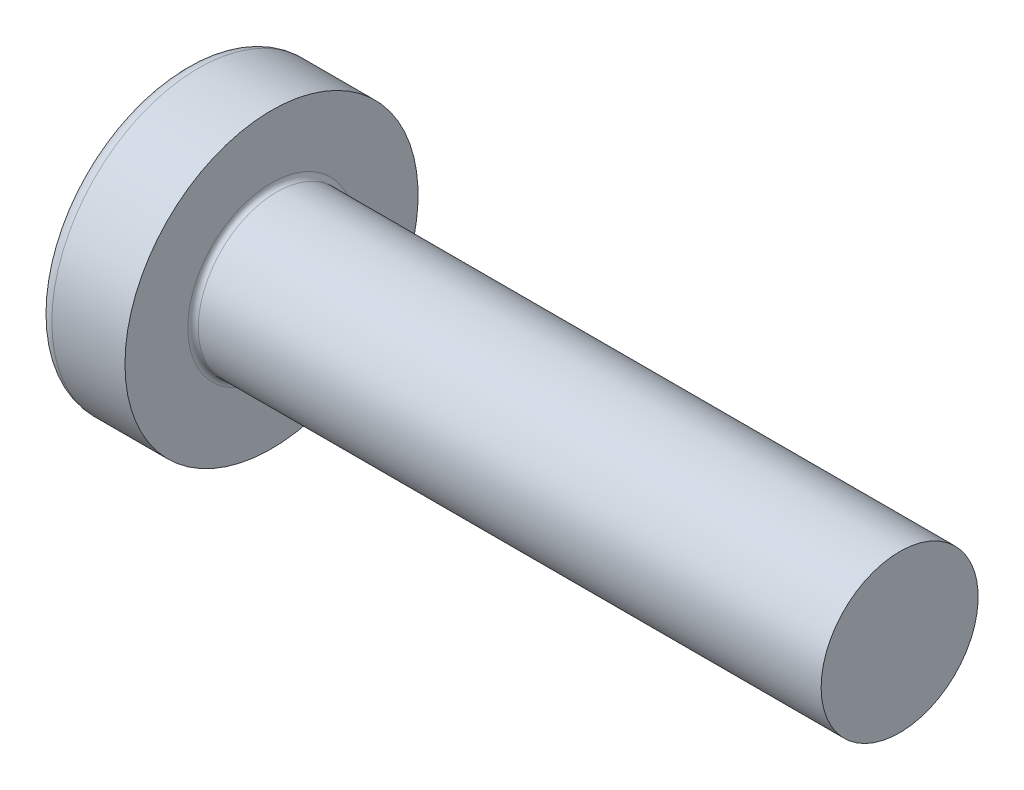
SolidWorks part; units mm, degrees
ref_plane "Plane1" through (0, 0, 0) normal (0, 0, 1) x (1, 0, 0)
ref_plane "Plane2" through (0, 0, 0) normal (0, 1, 0) x (1, 0, 0)
ref_plane "Plane3" through (0, 0, 0) normal (1, 0, 0) x (0, 0, -1)
sketch "BodySke" plane through (0, 0, 0) normal (0, 0, 1) x (1, 0, 0)
  line L0 (2.4, 1.5) -> (2.4, 2.8)
  line L1 (2.65, 6.35) -> (2.65, -3.175) construction
  line L2 (-25.4, 0) -> (127, 0) construction
  line L3 (14.4, 0) -> (0, 0)
  line L4 (2.4, 1.5) -> (14.4, 1.5)
  line L5 (14.4, 1.5) -> (14.4, 0)
  line L6 (1.0035, 2.8) -> (2.4, 2.8)
  line L8 (2.4, 6.35) -> (2.4, -3.175) construction
  arc A0 (0.7754, 2.6744) -> (0, 0) centre (5, 0) ccw
  arc A2 (0.7754, 2.6744) -> (1.0035, 2.8) centre (1.0035, 2.53) cw
  dimension "Head_fillet_rad" = 0.27
  dimension "Head_crown_rad" = 5
  dimension "Head_ht" = 2.4
  dimension "Diameter" = 3
  dimension "Length" = 12
  dimension "Head_dia" = 5.6
  dimension "Advance" = 0.5
  dimension "Thread_nom" = 12
revolve "Base-Revolve" add sketch "BodySke"
cosmetic thread "ThreadCosmetic" [suppressed]
fillet "Fillet1" radius 0.1 1 edges at (2.4, 0, 1.5)
sketch "Sketch3" plane through (0, 0, 0) normal (1, 0, 0) x (0, 0, -1)
  line L0 (0.37, -1.4) -> (-0.37, -1.4)
  line L1 (0.37, -1.4) -> (0.37, 1.4)
  line L2 (-0.37, 1.4) -> (0.37, 1.4)
  line L3 (-0.37, 1.4) -> (-0.37, -1.4)
  dimension "D1" = 1.4
  dimension "Cross_dia" = 2.8
  dimension "D2" = 0.37
  dimension "Cross_width" = 0.74
ref_plane "Plane4" through (1.75, 0, 0) normal (1, 0, 0) x (0, 0, -1)
sketch "Sketch4" plane through (1.75, 0, 0) normal (1, 0, 0) x (0, 0, -1)
  line L0 (0.37, -0.5275) -> (-0.37, -0.5275)
  line L1 (0.37, -0.5275) -> (0.37, 0.5275)
  line L2 (-0.37, 0.5275) -> (0.37, 0.5275)
  line L3 (-0.37, 0.5275) -> (-0.37, -0.5275)
  dimension "D1" = 0.74
  dimension "D2" = 1.055
  dimension "D3" = 0.37
  dimension "D4" = 0.5275
loft "Recess" cut profiles "Sketch3", "Sketch4"
pattern_circular "RecPat" count 2 every 90 about axis through (0, 0, 0) along (1, 0, 0) of "Recess"
sketch "RecCorSke" plane through (0, 0, 0) normal (0, 0, 1) x (1, 0, 0)
  line L0 (-3.175, 0) -> (15.875, 0) construction
  line L1 (-25.4, 0) -> (127, 0) construction
  line L2 (0, 0) -> (0, 0.6784)
  line L3 (0, 0.6784) -> (1.75, 0.556)
  line L4 (1.75, 0.556) -> (1.9307, 0)
  line L5 (1.9307, 0) -> (0, 0)
  dimension "Diameter" = 1.112
  dimension "Depth" = 1.75
  dimension "Draft_angle" = 4
  dimension "Bottom_angle" = 18
revolve "RecessCore" cut sketch "RecCorSke" angle 360 about L0
sketch "ThdSchSke" plane through (0, 0, 0) normal (0, 0, 1) x (1, 0, 0)
  line L0 (3.4, -1.2195) -> (3.2036, -1.5)
  line L1 (3.4, -1.2195) -> (3.5964, -1.5)
  line L2 (3.5964, -1.5) -> (3.5964, -1.875)
  line L3 (-3.175, 0) -> (5.1513, 0) construction
  line L5 (3.5964, -1.875) -> (3.2036, -1.875)
  line L6 (3.2036, -1.875) -> (3.2036, -1.5)
  dimension "Thread_minor" = 2.439
  dimension "Diameter" = 3
  dimension "Start" = 3.4
  dimension "SideAngle" = 55
  dimension "VeeAngle" = 70
  dimension "Overcut" = 3.75
revolve "ThreadSchematic" [suppressed] cut sketch "ThdSchSke" angle 360 about L3
pattern_linear "ThdSchPat" [suppressed]
equation "\"D1@Sketch3\" = \"Cross_dia@Sketch3\" / 2"
equation "\"D2@Sketch3\" = \"Cross_width@Sketch3\" / 2"
equation "\"Depth@RecCorSke\" = \"Cross_depth@Plane4\""
equation "\"D1@Sketch4\" = \"Cross_width@Sketch3\""
equation "\"D2@Sketch4\" = \"Cross_dia@Sketch3\" - 2.0 * \"Cross_depth@Plane4\" * tan(26.5  * 0.017453292)"
equation "\"D3@Sketch4\" = \"D1@Sketch4\" / 2"
equation "\"D4@Sketch4\" = \"D2@Sketch4\" / 2"
equation "\"Thread_length@ThreadCosmetic\" = ((sgn( (\"Length@BodySke\" - \"Advance@BodySke\" * 2.0 ) - \"Thread_nom@BodySke\" )-1)*( (\"Length@BodySke\" - \"Advance@BodySke\" * 2.0 ) - \"Thread_nom@BodySke\" ))/-2+ \"Thread_nom@BodySke\""
equation "\"Thread_minor@ThdSchSke\" = \"Thread_minor@ThreadCosmetic\""
equation "\"Diameter@ThdSchSke\" = \"Diameter@BodySke\""
equation "\"Overcut@ThdSchSke\" = \"Diameter@BodySke\" * 1.25"
equation "\"Start@ThdSchSke\" = \"Head_ht@BodySke\" + \"Length@BodySke\" - \"Thread_length@ThreadCosmetic\"  '---Non-countersunk---"
equation "\"Num_threads@ThdSchPat\" = int( \"Thread_length@ThreadCosmetic\" / \"Advance@BodySke\" + 0.999 )  + 1"
equation "\"Advance@ThdSchPat\" = \"Thread_length@ThreadCosmetic\" /  (\"Num_threads@ThdSchPat\" - 1) 'relax it"
